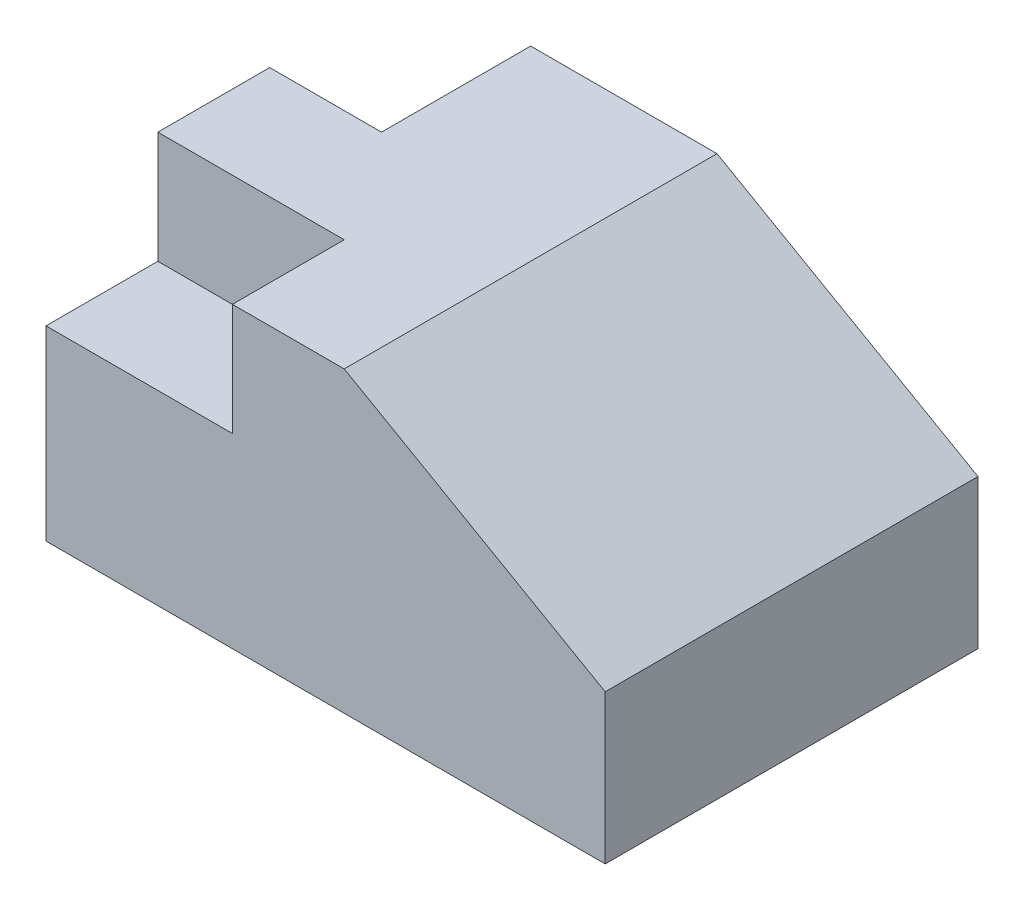
SolidWorks part; units mm, degrees
ref_plane "Front Plane" through (0, 0, 0) normal (0, 0, 1) x (1, 0, 0)
ref_plane "Top Plane" through (0, 0, 0) normal (0, 1, 0) x (1, 0, 0)
ref_plane "Right Plane" through (0, 0, 0) normal (1, 0, 0) x (0, 0, -1)
sketch "Sketch1" plane through (0, 0, 0) normal (0, 1, 0) x (1, 0, 0)
  line L1 (-75, -50) -> (75, -50)
  line L2 (-75, -50) -> (-75, 50)
  line L3 (-75, 50) -> (75, 50)
  line L4 (75, -50) -> (75, 50)
  line L5 (-75, -50) -> (75, 50) construction
  line L6 (-75, 50) -> (75, -50) construction
  point P0 (0, 0)
  dimension "D1" = 150
  dimension "D2" = 100
extrude "Boss-Extrude1" add sketch "Sketch1" along normal blind 80
sketch "Sketch2" plane through (0, 0, 50) normal (0, 0, 1) x (1, 0, 0)
  line L0 (5, 80) -> (75, 40)
  line L1 (-75, 80) -> (75, 80) construction
  line L2 (75, 80) -> (75, 0) construction
  line L3 (-75, 80) -> (-75, 0) construction
  line L8 (-75, 0) -> (75, 0)
  line L9 (75, 0) -> (75, 80)
  line L10 (75, 80) -> (-75, 80)
  line L11 (-75, 80) -> (-75, 0)
  line L12 (-75, 0) -> (75, 0)
  line L13 (75, 0) -> (75, 80)
  line L14 (75, 80) -> (-75, 80)
  line L15 (-75, 80) -> (-75, 0)
  line M6 (75, 0) -> (75, 80)
  line M7 (75, 80) -> (-75, 80)
  dimension "D1" = 80
  dimension "D2" = 40
  dimension "D3" = 0
extrude "Cut-Extrude1" cut sketch "Sketch2" against normal through all contours L0 M7 M6
sketch "Sketch3" plane through (0, 80, 0) normal (0, 1, 0) x (1, 0, 0)
  line L1 (-75, -50) -> (-25, -50)
  line L2 (-75, -50) -> (-75, -20)
  line L3 (-75, -20) -> (-25, -20)
  line L4 (-25, -50) -> (-25, -20)
  line L5 (-75, 50) -> (-45, 50)
  line L6 (-75, 50) -> (-75, 10)
  line L7 (-75, 10) -> (-45, 10)
  line L8 (-45, 50) -> (-45, 10)
  dimension "D1" = 50
  dimension "D2" = 30
  dimension "D3" = 40
  dimension "D4" = 30
extrude "Cut-Extrude2" cut sketch "Sketch3" against normal blind 30
